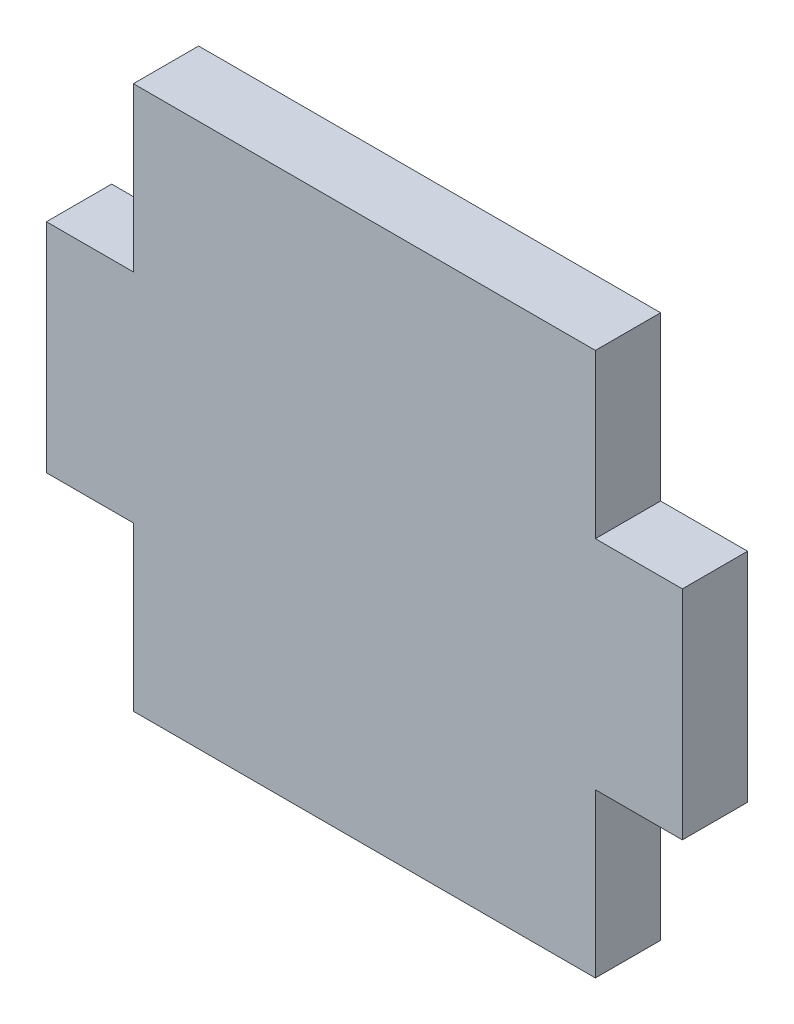
SolidWorks part; units mm, degrees
material "Balsa"
ref_plane "Alzado" through (0, 0, 0) normal (0, 0, 1) x (1, 0, 0)
ref_plane "Planta" through (0, 0, 0) normal (0, 1, 0) x (1, 0, 0)
ref_plane "Vista lateral" through (0, 0, 0) normal (1, 0, 0) x (0, 0, -1)
sketch "Croquis1" plane through (0, 0, 0) normal (0, 0, 1) x (1, 0, 0)
  line L0 (0, 0) -> (0, 7.5826) construction
  line L1 (-10.625, 12.5) -> (10.625, 12.5)
  line L2 (-10.625, 12.5) -> (-10.625, 5)
  line L3 (-10.625, -12.5) -> (10.625, -12.5)
  line L4 (10.625, 12.5) -> (10.625, 5)
  line L5 (-10.625, 12.5) -> (10.625, -12.5) construction
  line L6 (-10.625, -12.5) -> (10.625, 12.5) construction
  line L7 (10.625, 5) -> (14.625, 5)
  line L9 (10.625, -5) -> (14.625, -5)
  line L10 (14.625, 5) -> (14.625, -5)
  line L13 (10.625, -5) -> (10.625, -12.5)
  line L15 (-14.625, 5) -> (-14.625, -5)
  line L16 (-10.625, -5) -> (-14.625, -5)
  line L18 (-10.625, 5) -> (-14.625, 5)
  line L19 (10.625, -12.5) -> (-10.625, 12.5) construction
  line L20 (-10.625, -5) -> (-10.625, -12.5)
  point P0 (0, 0)
  point P6 (10.625, 0)
  point P17 (-10.625, 0)
  dimension "D1" = 21.25
  dimension "D2" = 25
  dimension "D3" = 10
extrude "Saliente-Extruir1" add sketch "Croquis1" along normal blind 3
